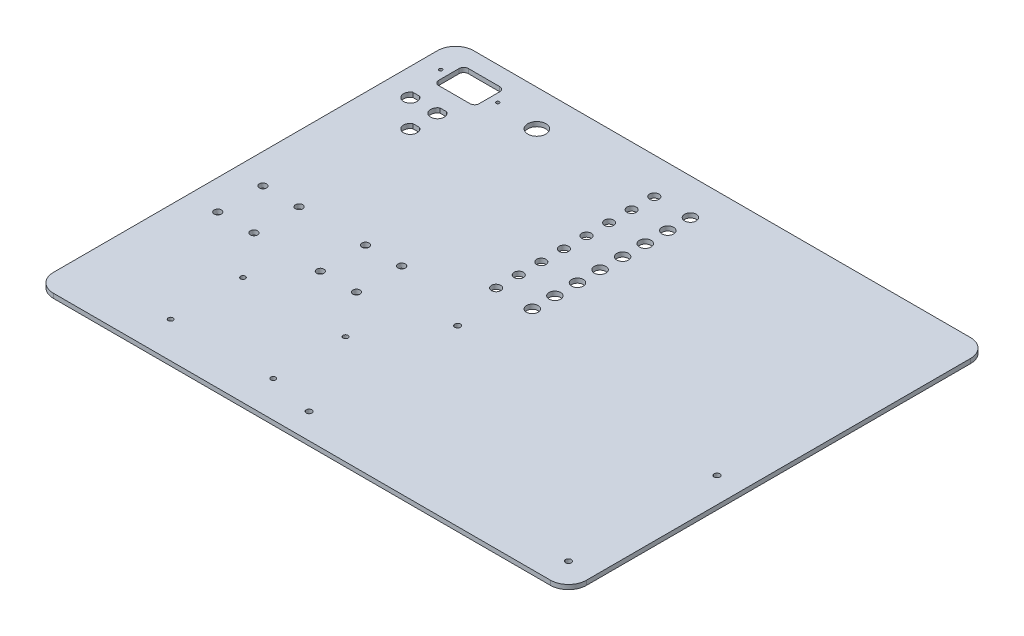
SolidWorks part; units mm, degrees
ref_plane "Front Plane" through (0, 0, 0) normal (0, 0, 1) x (1, 0, 0)
ref_plane "Top Plane" through (0, 0, 0) normal (0, 1, 0) x (1, 0, 0)
ref_plane "Right Plane" through (0, 0, 0) normal (1, 0, 0) x (0, 0, -1)
sketch "Sketch1" plane through (0, 0, 0) normal (0, 1, 0) x (1, 0, 0)
  line L1 (-187.325, 147.6375) -> (187.325, 147.6375)
  line L2 (-187.325, 147.6375) -> (-187.325, -147.6375)
  line L3 (-187.325, -147.6375) -> (187.325, -147.6375)
  line L4 (187.325, 147.6375) -> (187.325, -147.6375)
  line L5 (-187.325, 147.6375) -> (187.325, -147.6375) construction
  line L6 (-187.325, -147.6375) -> (187.325, 147.6375) construction
  point P0 (0, 0)
  dimension "D1" = 295.275
  dimension "D2" = 374.65
extrude "Boss-Extrude1" add sketch "Sketch1" along normal blind 3.175
fillet "Fillet1" radius 12.7 4 edges at (-187.325, 1.5875, -147.6375) (-187.325, 1.5875, 147.6375) (187.325, 1.5875, -147.6375) (187.325, 1.5875, 147.6375)
extrude "Cut-Extrude1" cut sketch "Sketch2" against normal through all
sketch "Sketch2" plane through (0, 3.175, 0) normal (0, 1, 0) x (1, 0, 0)
  line L0 (-22.2522, 122.2375) -> (-22.2522, 106.3625) construction
  line L1 (-22.2522, 106.3625) -> (-22.2522, 90.4875) construction
  line L2 (-22.2522, 90.4875) -> (-22.2522, 74.6125) construction
  line L3 (-22.2522, 74.6125) -> (-22.2522, 58.7375) construction
  line L4 (-22.2522, 58.7375) -> (-22.2522, 42.8625) construction
  line L5 (-22.2522, 42.8625) -> (-22.2522, 26.9875) construction
  line L6 (-22.2522, 26.9875) -> (-22.2522, 11.1125) construction
  circle A0 centre (-22.2522, 122.2375) radius 3.2639
  circle A1 centre (-22.2522, 106.3625) radius 3.2639
  circle A2 centre (-22.2522, 90.4875) radius 3.2639
  circle A3 centre (-22.2522, 74.6125) radius 3.2639
  circle A4 centre (-22.2522, 58.7375) radius 3.2639
  circle A5 centre (-22.2522, 42.8625) radius 3.2639
  circle A6 centre (-22.2522, 26.9875) radius 3.2639
  circle A7 centre (-22.2522, 11.1125) radius 3.2639
  circle A9 centre (3.1478, 122.2375) radius 4.1021
  circle A10 centre (3.1478, 106.3625) radius 4.1021
  circle A11 centre (3.1478, 90.4875) radius 4.1021
  circle A12 centre (3.1478, 74.6125) radius 4.1021
  circle A13 centre (3.1478, 58.7375) radius 4.1021
  circle A14 centre (3.1478, 42.8625) radius 4.1021
  circle A15 centre (3.1478, 26.9875) radius 4.1021
  circle A16 centre (3.1478, 11.1125) radius 4.1021
sketch "Sketch3" plane through (0, 3.175, 0) normal (0, 1, 0) x (1, 0, 0)
  line L0 (174.625, 147.6375) -> (-174.625, 147.6375) construction
  line L1 (-168.8465, 134.9375) -> (-140.3985, 134.9375)
  line L2 (-168.8465, 134.9375) -> (-168.8465, 114.1095)
  line L3 (-168.8465, 114.1095) -> (-140.3985, 114.1095)
  line L4 (-140.3985, 134.9375) -> (-140.3985, 114.1095)
  line L5 (-168.8465, 134.9375) -> (-140.3985, 114.1095) construction
  line L6 (-168.8465, 114.1095) -> (-140.3985, 134.9375) construction
  line L7 (-174.625, 124.5235) -> (-134.62, 124.5235) construction
  line L8 (-187.325, 134.9375) -> (-187.325, -134.9375) construction
  point P0 (-154.6225, 124.5235)
  point P7 (-174.625, 124.5235)
  point P8 (-134.62, 124.5235)
  dimension "D1" = 28.448
  dimension "D2" = 20.828
  dimension "D3" = 12.7
  dimension "D4" = 40.005
  dimension "D5" = 12.7
extrude "Cut-Extrude2" cut sketch "Sketch3" against normal through all
hole_wizard "#4-40 Tapped Hole1" positions "Sketch4" profile "Sketch5" tap size "#4-40" standard "ANSI Inch" end condition through all
sketch "Sketch4" plane through (0, 3.175, 0) normal (0, 1, 0) x (1, 0, 0)
  point P0 (-174.625, 124.5235)
  point P3 (-134.62, 124.5235)
sketch "Sketch5" plane through (-174.625, 3.175, -124.5235) normal (1, 0, 0) x (0, 0, 1)
  line L0 (0, 0) -> (0, 3.175)
  line L1 (0, 3.175) -> (1.1303, 3.175)
  line L2 (1.1303, 3.175) -> (1.1303, 0)
  line L5 (1.1303, 0) -> (0, 0)
  line L11 (0, -6.35) -> (0, 107.95) construction
  dimension "Thru Tap Drill Dia." = 2.2606
  dimension "Thru Tap Drill Depth" = 3.175
cosmetic thread "Hole Thread1" parameters "D2"=2.8448
cosmetic thread "Hole Thread2" parameters "D2"=2.8448
fillet "Fillet2" radius 3.175 4 edges at (-168.8465, 1.5875, -114.1095) (-140.3985, 1.5875, -114.1095) (-140.3985, 1.5875, -134.9375) (-168.8465, 1.5875, -134.9375)
sketch "Sketch6" plane through (0, 3.175, 0) normal (0, 1, 0) x (1, 0, 0)
  line L0 (-170.651, 100.965) -> (-165.899, 100.965)
  line L1 (-151.601, 100.965) -> (-146.849, 100.965)
  line L2 (-151.601, 81.915) -> (-146.849, 81.915)
  line L3 (174.625, 147.6375) -> (-174.625, 147.6375) construction
  line L5 (-187.325, 134.9375) -> (-187.325, -134.9375) construction
  arc A0 (-170.651, 100.965) -> (-165.899, 100.965) centre (-168.275, 96.8375) ccw
  arc A1 (-151.601, 100.965) -> (-146.849, 100.965) centre (-149.225, 96.8375) ccw
  arc A2 (-151.601, 81.915) -> (-146.849, 81.915) centre (-149.225, 77.7875) ccw
  dimension "D1" = 9.525
  dimension "D2" = 19.05
  dimension "D3" = 19.05
  dimension "D4" = 8.89
  dimension "D5" = 50.8
  dimension "D6" = 19.05
extrude "Cut-Extrude3" cut sketch "Sketch6" against normal through all
sketch "Sketch7" plane through (0, 3.175, 0) normal (0, 1, 0) x (1, 0, 0)
  line L0 (174.625, 147.6375) -> (-174.625, 147.6375) construction
  line L1 (-187.325, 134.9375) -> (-187.325, -134.9375) construction
  circle A0 centre (-104.775, 122.2375) radius 6.35
  dimension "D1" = 12.7
  dimension "D2" = 25.4
  dimension "D3" = 82.55
extrude "Cut-Extrude4" cut sketch "Sketch7" against normal through all
hole_wizard "#10-32 Tapped Hole" positions "Sketch8" profile "Sketch9" tap size "#10-32" standard "ANSI Inch" end condition through all
sketch "Sketch8" plane through (0, 3.175, 0) normal (0, 1, 0) x (1, 0, 0)
  point P0 (169.4225, -25.341)
  point P2 (-12.8479, -25.341)
  point P4 (-12.8479, -129.735)
  point P6 (169.4225, -129.735)
  point P9 (0, 0)
  point P12 (0, 0)
  point P15 (0, 0)
  point P18 (0, 0)
sketch "Sketch9" plane through (169.4225, 3.175, 25.341) normal (1, 0, 0) x (0, 0, 1)
  line L0 (0, 0) -> (0, 3.175)
  line L1 (0, 3.175) -> (2.0193, 3.175)
  line L2 (2.0193, 3.175) -> (2.0193, 0)
  line L3 (2.0193, 0) -> (0, 0)
  line L4 (0, -6.35) -> (0, 107.95) construction
  dimension "Thru Tap Drill Dia." = 4.0386
  dimension "Thru Tap Drill Depth" = 3.175
cosmetic thread "Hole Thread7" parameters "D2"=4.826
cosmetic thread "Hole Thread8" parameters "D2"=4.826
cosmetic thread "Hole Thread9" parameters "D2"=4.826
cosmetic thread "Hole Thread10" parameters "D2"=4.826
hole_wizard "#8-32 Tapped Hole1" positions "Sketch10" profile "Sketch11" tap size "#8-32" standard "ANSI Inch" end condition through all
sketch "Sketch10" plane through (0, 3.175, 0) normal (0, 1, 0) x (1, 0, 0)
  point P0 (-117.5856, -122.2756)
  point P2 (-117.5856, -71.4756)
  point P4 (-45.5068, -71.4756)
  point P6 (-45.5068, -122.2756)
  point P9 (0, 0)
  point P12 (0, 0)
  point P15 (0, 0)
  point P18 (0, 0)
sketch "Sketch11" plane through (-117.5856, 3.175, 122.2756) normal (1, 0, 0) x (0, 0, 1)
  line L0 (0, 0) -> (0, 3.175)
  line L1 (0, 3.175) -> (1.7272, 3.175)
  line L2 (1.7272, 3.175) -> (1.7272, 0)
  line L3 (1.7272, 0) -> (0, 0)
  line L4 (0, -6.35) -> (0, 107.95) construction
  dimension "Thru Tap Drill Dia." = 3.4544
  dimension "Thru Tap Drill Depth" = 3.175
cosmetic thread "Hole Thread3" parameters "D2"=4.1656
cosmetic thread "Hole Thread4" parameters "D2"=4.1656
cosmetic thread "Hole Thread5" parameters "D2"=4.1656
cosmetic thread "Hole Thread6" parameters "D2"=4.1656
hole_wizard "#10 Clearance Hole2" positions "Sketch12" profile "Sketch13" hole size "#10" standard "ANSI Inch" end condition through all
sketch "Sketch12" plane through (0, 0, 0) normal (0, -1, 0) x (-1, 0, 0)
  point P1 (140.925, -8.7025)
  point P3 (166.325, -8.7025)
  point P5 (166.325, -40.4525)
  point P7 (140.925, -40.4525)
  point P9 (94.2462, -40.4525)
  point P11 (94.2462, -8.7025)
  point P13 (68.8462, -8.7025)
  point P15 (68.8462, -40.4525)
  point P20 (0, 0)
  point P23 (0, 0)
  point P26 (0, 0)
  point P29 (0, 0)
  point P32 (0, 0)
  point P35 (0, 0)
  point P38 (0, 0)
sketch "Sketch13" plane through (-140.925, 0, 8.7025) normal (1, 0, 0) x (0, 0, -1)
  line L0 (0, 0) -> (0, 3.175)
  line L1 (0, 3.175) -> (2.5527, 3.175)
  line L2 (2.5527, 3.175) -> (2.5527, 0)
  line L3 (2.5527, 0) -> (0, 0)
  line L4 (0, -6.35) -> (0, 107.95) construction
  dimension "Thru Hole Dia." = 5.1054
  dimension "Thru Hole Depth" = 3.175
